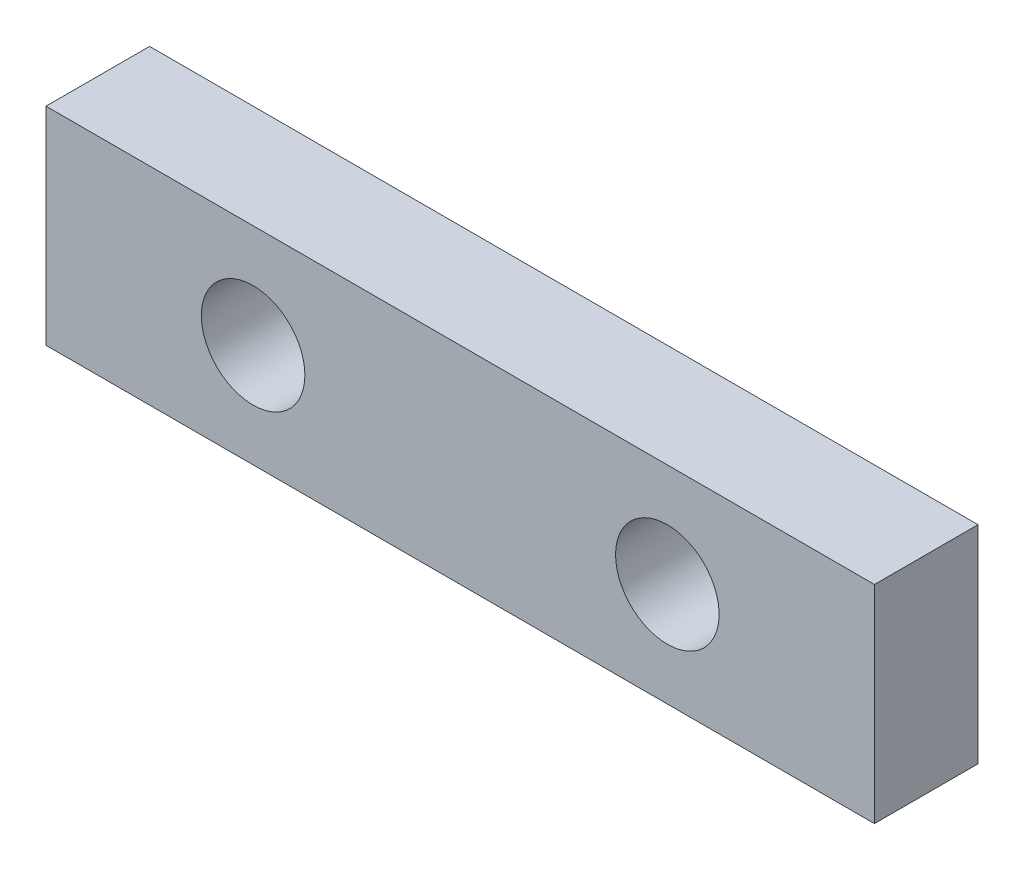
SolidWorks part; units mm, degrees
ref_plane "Front Plane" through (0, 0, 0) normal (0, 0, 1) x (1, 0, 0)
ref_plane "Top Plane" through (0, 0, 0) normal (0, 1, 0) x (1, 0, 0)
ref_plane "Right Plane" through (0, 0, 0) normal (1, 0, 0) x (0, 0, -1)
sketch "Sketch1" plane through (0, 0, 0) normal (0, 0, 1) x (1, 0, 0)
  line L0 (0, 0) -> (0, 5) construction
  line L1 (-20, 5) -> (20, 5)
  line L2 (-20, 5) -> (-20, -5)
  line L3 (-20, -5) -> (20, -5)
  line L4 (20, 5) -> (20, -5)
  line L5 (-20, 5) -> (20, -5) construction
  line L6 (-20, -5) -> (20, 5) construction
  circle A0 centre (-10, 0) radius 2.5
  circle A1 centre (10, 0) radius 2.5
  point P0 (0, 0)
  dimension "D4" = 5
  dimension "D1" = 40
  dimension "D2" = 10
  dimension "D3" = 10
extrude "Boss-Extrude1" add sketch "Sketch1" along normal blind 5
